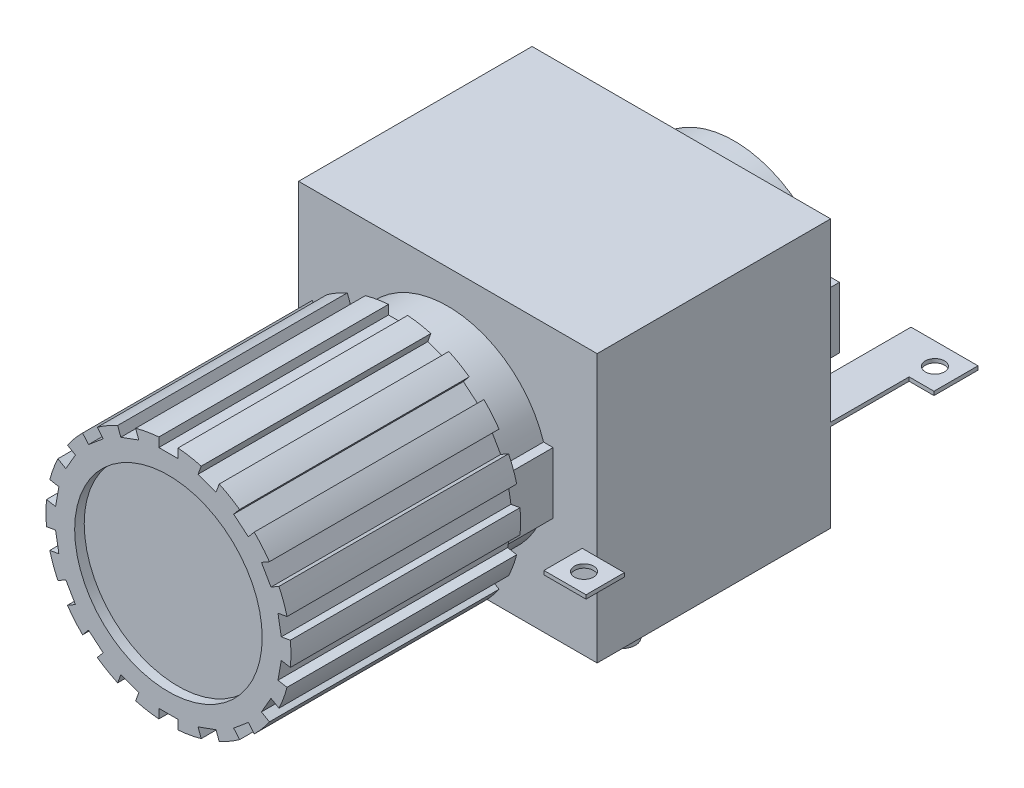
SolidWorks part; units mm, degrees
ref_plane "Alzado" through (0, 0, 0) normal (0, 0, 1) x (1, 0, 0)
ref_plane "Planta" through (0, 0, 0) normal (0, 1, 0) x (1, 0, 0)
ref_plane "Vista lateral" through (0, 0, 0) normal (1, 0, 0) x (0, 0, -1)
sketch "Croquis1" plane through (0, 0, 0) normal (0, 0, 1) x (1, 0, 0)
  circle A0 centre (0, 0) radius 32
  dimension "D1" = 64
extrude "Saliente-Extruir1" add sketch "Croquis1" along normal blind 60
sketch "Croquis2" plane through (0, 0, 60) normal (0, 0, 1) x (1, 0, 0)
  circle A0 centre (0, 0) radius 24.5
  dimension "D1" = 49
extrude "Cortar-Extruir1" cut sketch "Croquis2" against normal blind 2.5
sketch "Croquis3" plane through (0, 0, 60) normal (0, 0, 1) x (1, 0, 0)
  line L1 (-2.5, 34.5) -> (2.5, 34.5)
  line L2 (-2.5, 34.5) -> (-2.5, 29.5)
  line L3 (-2.5, 29.5) -> (2.5, 29.5)
  line L4 (2.5, 34.5) -> (2.5, 29.5)
  line L5 (-2.5, 34.5) -> (2.5, 29.5) construction
  line L6 (-2.5, 29.5) -> (2.5, 34.5) construction
  circle A0 centre (0, 0) radius 32 construction
  point P0 (0, 32)
  dimension "D1" = 5
  dimension "D2" = 5
extrude "Cortar-Extruir2" cut sketch "Croquis3" against normal through all
pattern_circular "MatrizC1" count 18 over 360 about axis through (0, 0, 0) along (0, 0, 1) of "Cortar-Extruir2"
sketch "Croquis4" plane through (0, 0, 0) normal (0, 0, -1) x (-1, 0, 0)
  circle A0 centre (0, 0) radius 26.25
  dimension "D1" = 52.5
extrude "Saliente-Extruir2" add sketch "Croquis4" along normal blind 87.8
sketch "Croquis5" plane through (0, 0, -87.8) normal (0, 0, -1) x (-1, 0, 0)
  circle A0 centre (0, 0) radius 22.75
  circle A1 centre (0, 0) radius 26.25 construction
  dimension "D1" = 3.5
extrude "Cortar-Extruir3" cut sketch "Croquis5" against normal blind 37
sketch "Croquis6" plane through (0, 0, -87.8) normal (0, 0, -1) x (-1, 0, 0)
  line L0 (0, 0) -> (-26.25, 0) construction
  line L2 (-27.5, 8) -> (-25, 8)
  line L3 (-27.5, 8) -> (-27.5, -8)
  line L4 (-27.5, -8) -> (-25, -8)
  line L5 (-25, 8) -> (-25, -8)
  line L6 (-27.5, 8) -> (-25, -8) construction
  line L7 (-27.5, -8) -> (-25, 8) construction
  circle A0 centre (0, 0) radius 26.25 construction
  dimension "D1" = 2.5
  dimension "D2" = 16
extrude "Saliente-Extruir3" add sketch "Croquis6" against normal up to next
ref_plane "Plano1" through (0, 0, -13) normal (0, 0, -1) x (-1, 0, 0)
sketch "Croquis7" plane through (0, 0, -13) normal (0, 0, -1) x (-1, 0, 0)
  line L1 (-39, 35) -> (39, 35)
  line L2 (-39, 35) -> (-39, -35)
  line L3 (-39, -35) -> (39, -35)
  line L4 (39, 35) -> (39, -35)
  line L5 (-39, 35) -> (39, -35) construction
  line L6 (-39, -35) -> (39, 35) construction
  point P0 (0, 0)
  dimension "D1" = 78
  dimension "D2" = 70
extrude "Saliente-Extruir4" add sketch "Croquis7" along normal blind 61
sketch "Croquis8" plane through (-39, 0, 0) normal (-1, 0, 0) x (0, 0, 1)
  line L0 (-74, 35) -> (-13, 35) construction
  line L1 (-59.8, -11) -> (-69.8, -11)
  line L2 (-59.8, -11) -> (-59.8, -12)
  line L3 (-59.8, -12) -> (-69.8, -12)
  line L4 (-69.8, -11) -> (-69.8, -12)
  line L5 (-3, -7) -> (-13, -7)
  line L6 (-3, -7) -> (-3, -8)
  line L7 (-3, -8) -> (-13, -8)
  line L8 (-13, -7) -> (-13, -8)
  line L9 (-13, -35) -> (-13, 35) construction
  line L10 (-74, -35) -> (-74, 35) construction
  dimension "D1" = 10
  dimension "D2" = 10
  dimension "D3" = 1
  dimension "D4" = 1
  dimension "D5" = 47
  dimension "D6" = 43
  dimension "D7" = 14.2
extrude "Saliente-Extruir5" add sketch "Croquis8" along normal blind 11.5
sketch "Croquis9" plane through (-39, 0, 0) normal (-1, 0, 0) x (0, 0, 1)
  line L0 (-13, -35) -> (-13, 35) construction
  line L1 (-3, -8) -> (-13, -8)
  line L2 (-3, -8) -> (-3, 5)
  line L3 (-3, 5) -> (-13, 5)
  line L4 (-13, -8) -> (-13, 5)
  dimension "D1" = 13
extrude "Saliente-Extruir6" add sketch "Croquis9" against normal blind 1
ref_plane "Plano2" through (0, -11, 0) normal (0, -1, 0) x (-1, 0, 0)
sketch "Croquis10" plane through (0, -11, 0) normal (0, -1, 0) x (-1, 0, 0)
  line L0 (39, 13) -> (-39, 13) construction
  line L1 (-35.1, 13) -> (-46.1, 13)
  line L2 (-35.1, 13) -> (-35.1, 3)
  line L3 (-35.1, 3) -> (-46.1, 3)
  line L4 (-46.1, 13) -> (-46.1, 3)
  line L6 (-27.5, 0) -> (-27.5, 13) construction
  dimension "D1" = 11
  dimension "D2" = 10
  dimension "D3" = 7.6
extrude "Saliente-Extruir7" add sketch "Croquis10" along normal blind 1
sketch "Croquis11" plane through (0, -11, 0) normal (0, -1, 0) x (-1, 0, 0)
  line L1 (-39, 74) -> (-28, 74)
  line L2 (-39, 74) -> (-39, 94.5)
  line L3 (-45.5, 106) -> (-28, 106)
  line L4 (-28, 74) -> (-28, 106)
  line L7 (-39, 94.5) -> (-45.5, 94.5)
  line L8 (-45.5, 106) -> (-45.5, 94.5)
  dimension "D1" = 32
  dimension "D2" = 17.5
  dimension "D3" = 6.5
  dimension "D4" = 11.5
extrude "Saliente-Extruir8" add sketch "Croquis11" along normal blind 1
sketch "Croquis12" plane through (0, -7, 0) normal (0, 1, 0) x (1, 0, 0)
  circle A0 centre (-44.75, 7.9491) radius 2.5
  dimension "D1" = 5
extrude "Cortar-Extruir4" cut sketch "Croquis12" against normal through all
sketch "Croquis13" plane through (0, -11, 0) normal (0, 1, 0) x (1, 0, 0)
  circle A0 centre (40.6, 7.9786) radius 2.5
  dimension "D1" = 5
extrude "Cortar-Extruir5" cut sketch "Croquis13" against normal blind 1
sketch "Croquis14" plane through (0, -11, 0) normal (0, 1, 0) x (1, 0, 0)
  circle A0 centre (-44.75, 65.0495) radius 2.5
  dimension "D1" = 5
extrude "Cortar-Extruir6" cut sketch "Croquis14" against normal blind 1
sketch "Croquis15" plane through (0, -11, 0) normal (0, 1, 0) x (1, 0, 0)
  line L0 (45.5, 100.25) -> (40, 100.25) construction
  line L1 (45.5, 106) -> (45.5, 94.5) construction
  circle A0 centre (40, 100.25) radius 2.5
  point P6 (0, 0)
  dimension "D1" = 5
  dimension "D2" = 5.5
extrude "Cortar-Extruir7" cut sketch "Croquis15" against normal blind 1
sketch "Croquis16" plane through (0, -35, 0) normal (0, -1, 0) x (-1, 0, 0)
  line L0 (-39, 74) -> (-39, 13) construction
  line L1 (-39, 13) -> (39, 13) construction
  circle A0 centre (-26.5, 32) radius 3.5
  dimension "D1" = 7
  dimension "D2" = 12.5
  dimension "D3" = 19
extrude "Saliente-Extruir9" add sketch "Croquis16" along normal blind 10
